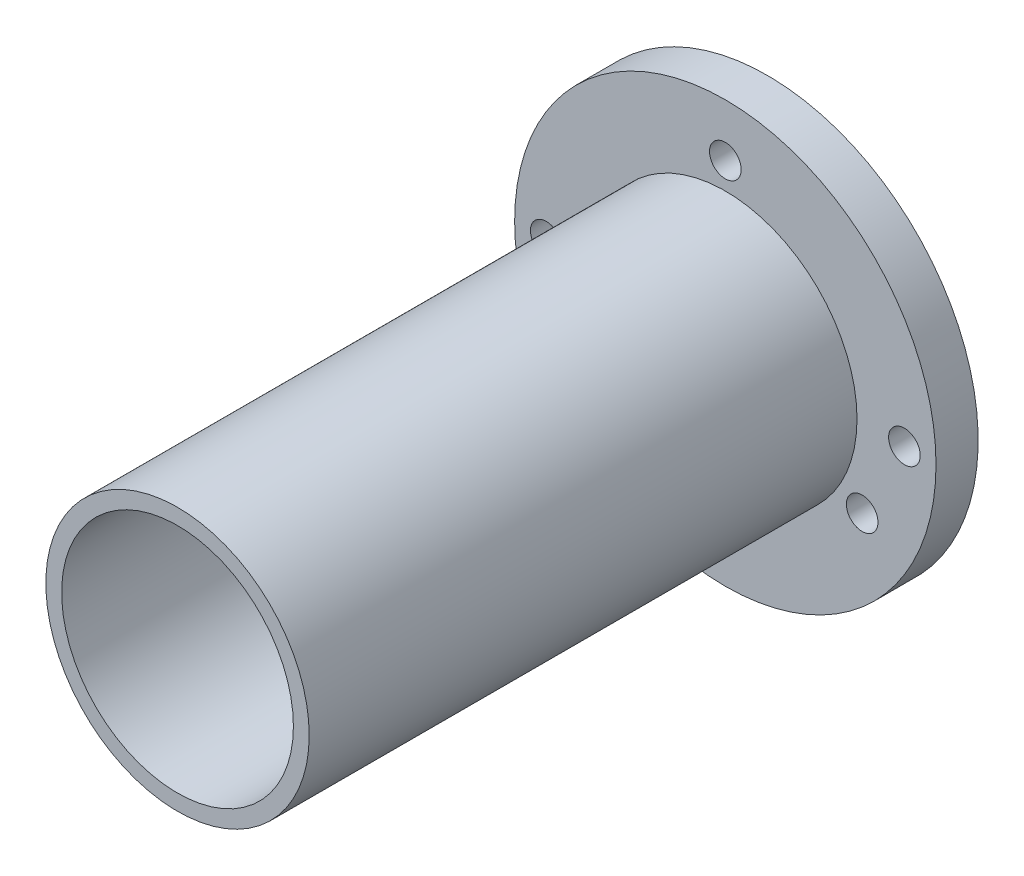
SolidWorks part; units mm, degrees
ref_plane "Front Plane" through (0, 0, 0) normal (0, 0, 1) x (1, 0, 0)
ref_plane "Top Plane" through (0, 0, 0) normal (0, 1, 0) x (1, 0, 0)
ref_plane "Right Plane" through (0, 0, 0) normal (1, 0, 0) x (0, 0, -1)
sketch "Sketch1" plane through (0, 0, 0) normal (0, 0, 1) x (1, 0, 0)
  circle A0 centre (0, 0) radius 5.5
  circle A1 centre (0, 0) radius 10
  dimension "D1" = 11
  dimension "D2" = 20
extrude "Boss-Extrude1" add sketch "Sketch1" along normal blind 2
sketch "Sketch3" plane through (0, 0, 0) normal (0, 0, -1) x (-1, 0, 0)
  circle A0 centre (0, 0) radius 3
  dimension "D1" = 6
extrude "Boss-Extrude2" add sketch "Sketch3" along normal blind 12 separate body
sketch "Sketch4" plane through (0, 0, 0) normal (0, 0, -1) x (-1, 0, 0)
  circle A0 centre (0, 0) radius 10 construction
  circle A2 centre (0, 0) radius 10
  circle A4 centre (0, 0) radius 3 construction
  circle A5 centre (0, 0) radius 3
extrude "Boss-Extrude3" add sketch "Sketch4" along normal blind 2
chamfer "Chamfer2" distance 1 angle 45 1 edges at (-3, 0, -2)
chamfer "Chamfer4" distance 0.5 angle 45 1 edges at (-3, 0, -12)
sketch "Sketch5" plane through (0, 0, -2) normal (0, 0, -1) x (-1, 0, 0)
  line L0 (-10, 0) -> (10, 0) construction
  circle A0 centre (0, 0) radius 10 construction
  circle A1 centre (-8.5, 0) radius 0.75
  circle A2 centre (8.5, 0) radius 0.75
  circle A3 centre (0, 0) radius 4 construction
  point P9 (4, 0)
  dimension "D1" = 1.5
  dimension "D2" = 1.5
  dimension "D3" = 1.5
  dimension "D4" = 1.5
extrude "Cut-Extrude1" cut sketch "Sketch5" against normal up to next
sketch "Sketch6" plane through (0, 0, 2) normal (0, 0, 1) x (1, 0, 0)
  circle A0 centre (0, 0) radius 6.25
  circle A1 centre (0, 0) radius 5.5 construction
  circle A2 centre (0, 0) radius 5.5
  dimension "D1" = 0.75
extrude "Boss-Extrude4" add sketch "Sketch6" along normal blind 26
sketch "Sketch7" plane through (0, 0, -2) normal (0, 0, -1) x (-1, 0, 0)
  circle A0 centre (0, 0) radius 7.5 construction
  circle A1 centre (0, 7.5) radius 0.75
  circle A2 centre (6.4952, -3.75) radius 0.75
  circle A3 centre (-6.4952, -3.75) radius 0.75
  point P14 (0, 0)
  dimension "D1" = 15
  dimension "D2" = 1.5
  dimension "D3" = 3
extrude "Cut-Extrude2" cut sketch "Sketch7" against normal up to next
sketch "Sketch8" plane through (0, 0, -12) normal (0, 0, -1) x (-1, 0, 0)
  circle A0 centre (0, 0) radius 16.6145
extrude "Cut-Extrude3" cut sketch "Sketch8" against normal blind 12
